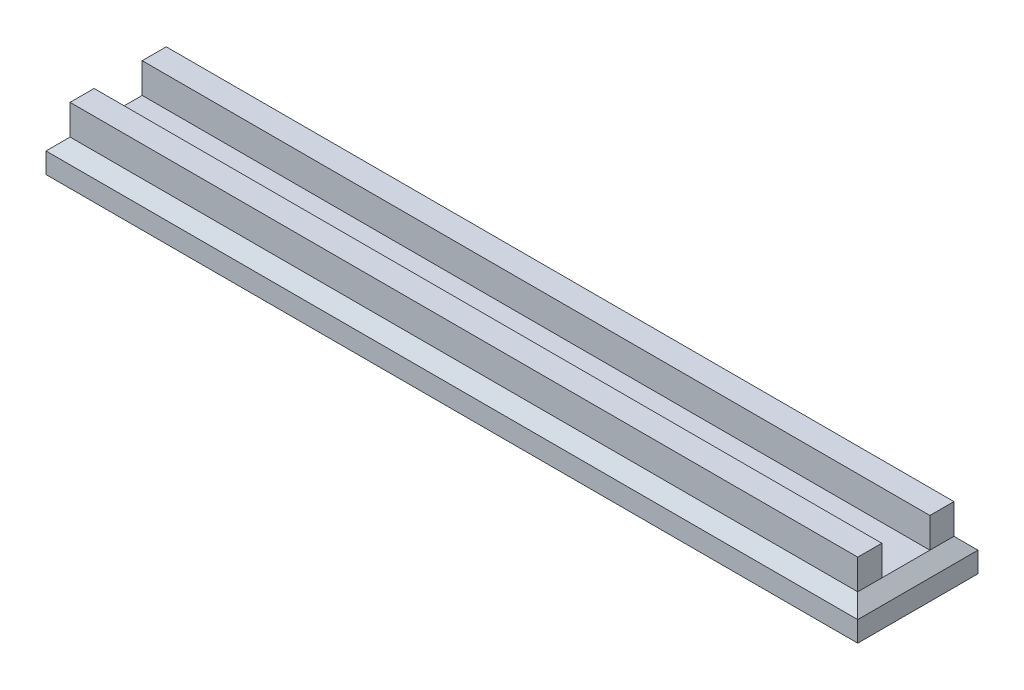
SolidWorks part; units mm, degrees
ref_plane "Front Plane" through (0, 0, 0) normal (0, 0, 1) x (1, 0, 0)
ref_plane "Top Plane" through (0, 0, 0) normal (0, 1, 0) x (1, 0, 0)
ref_plane "Right Plane" through (0, 0, 0) normal (1, 0, 0) x (0, 0, -1)
sketch "Sketch1" plane through (0, 0, 0) normal (0, 1, 0) x (1, 0, 0)
  line L1 (-67.5, -10) -> (67.5, -10)
  line L2 (-67.5, -10) -> (-67.5, 10)
  line L3 (-67.5, 10) -> (67.5, 10)
  line L4 (67.5, -10) -> (67.5, 10)
  line L5 (-67.5, -10) -> (67.5, 10) construction
  line L6 (-67.5, 10) -> (67.5, -10) construction
  point P0 (0, 0)
  dimension "D1" = 135
  dimension "D2" = 20
extrude "Boss-Extrude1" add sketch "Sketch1" along normal blind 5.4
chamfer "Chamfer1" distance 2 angle 45 4 edges at (0, 5.4, 10) (-67.5, 5.4, 0) (0, 5.4, -10) (67.5, 5.4, 0)
sketch "Sketch2" plane through (0, 5.4, 0) normal (0, 1, 0) x (1, 0, 0)
  line L0 (65.5, -8) -> (65.5, 8) construction
  line L1 (-65.5, 8) -> (65.5, 8)
  line L2 (-65.5, 8) -> (-65.5, 4)
  line L3 (-65.5, 4) -> (65.5, 4)
  line L4 (65.5, 8) -> (65.5, 4)
  line L5 (-65.5, 0) -> (65.5, 0) construction
  line L6 (-65.5, 8) -> (-65.5, -8) construction
  line L7 (-65.5, -4) -> (65.5, -4)
  line L8 (65.5, -8) -> (65.5, -4)
  line L9 (-65.5, -8) -> (65.5, -8)
  line L10 (-65.5, -8) -> (-65.5, -4)
  dimension "D1" = 4
extrude "Boss-Extrude2" add sketch "Sketch2" along normal blind 5
